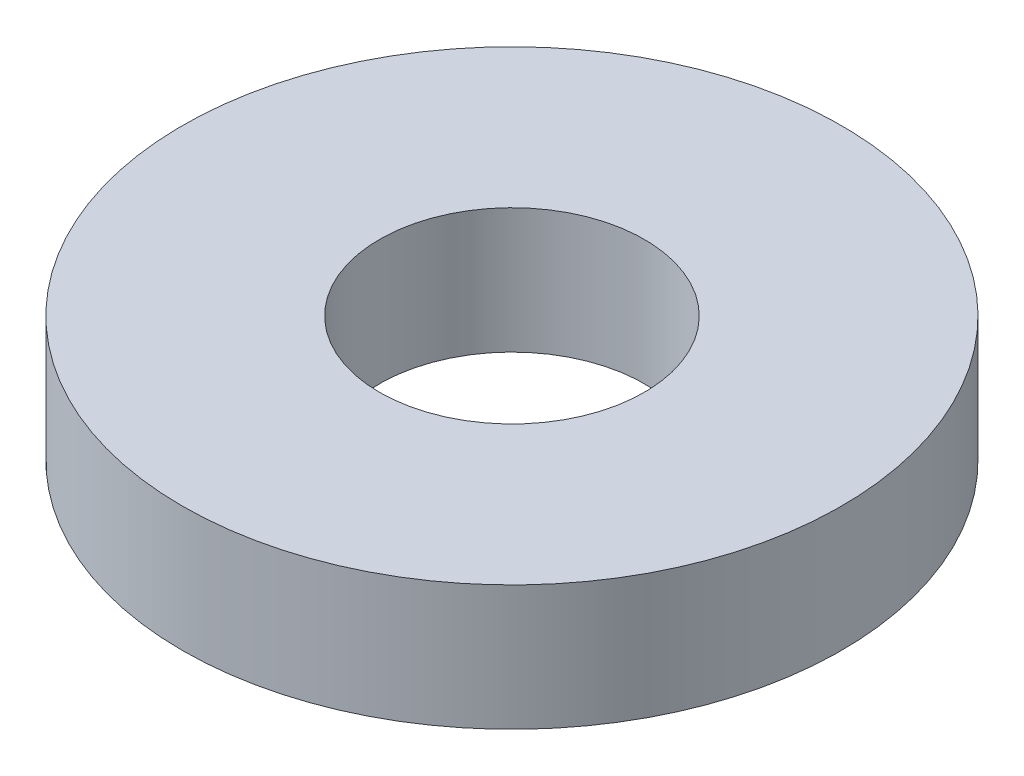
SolidWorks part; units mm, degrees
material "AISI 1020"
ref_plane "Front Plane" through (0, 0, 0) normal (0, 0, 1) x (1, 0, 0)
ref_plane "Top Plane" through (0, 0, 0) normal (0, 1, 0) x (1, 0, 0)
ref_plane "Right Plane" through (0, 0, 0) normal (1, 0, 0) x (0, 0, -1)
sketch "Sketch1" plane through (0, 0, 0) normal (0, 1, 0) x (1, 0, 0)
  circle A0 centre (-5.9123, 13.8633) radius 7.8994
  circle A1 centre (-5.9123, 13.8633) radius 3.175
extrude "Extrude1" add sketch "Sketch1" along normal blind 2.9972
